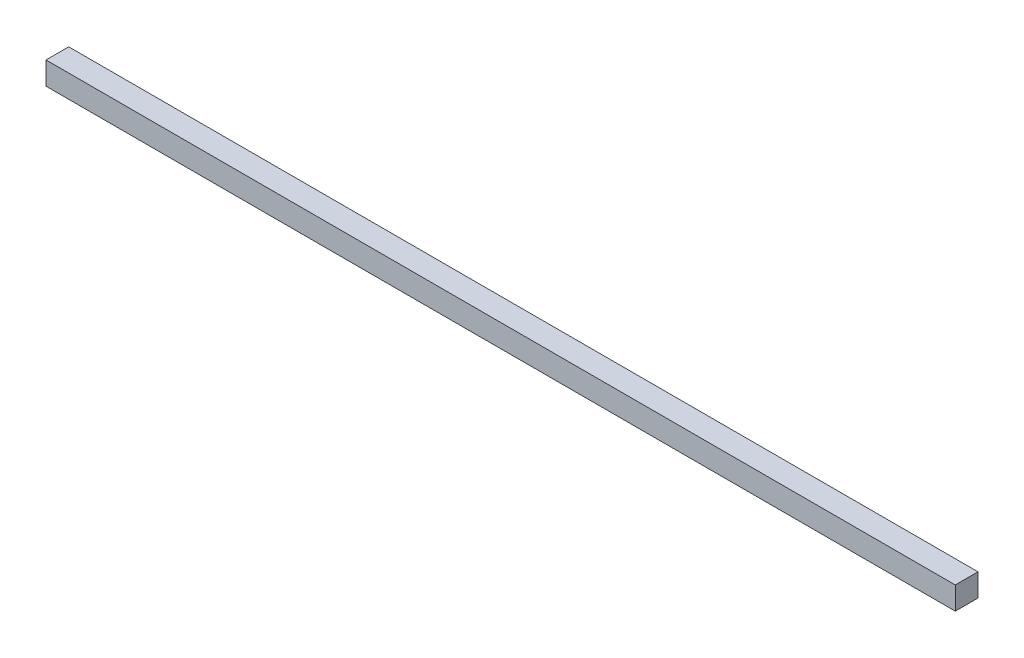
SolidWorks part; units mm, degrees
ref_plane "Front Plane" through (0, 0, 0) normal (0, 0, 1) x (1, 0, 0)
ref_plane "Top Plane" through (0, 0, 0) normal (0, 1, 0) x (1, 0, 0)
ref_plane "Right Plane" through (0, 0, 0) normal (1, 0, 0) x (0, 0, -1)
sketch "Sketch1" plane through (0, 0, 0) normal (0, 1, 0) x (1, 0, 0)
  line L0 (-200, 5) -> (200, -5) construction
  line L1 (-200, 5) -> (200, 5)
  line L2 (-200, 5) -> (-200, -5)
  line L3 (-200, -5) -> (200, -5)
  line L4 (200, 5) -> (200, -5)
  dimension "D1" = 400
  dimension "D2" = 10
extrude "Boss-Extrude1" add sketch "Sketch1" along normal blind 10
